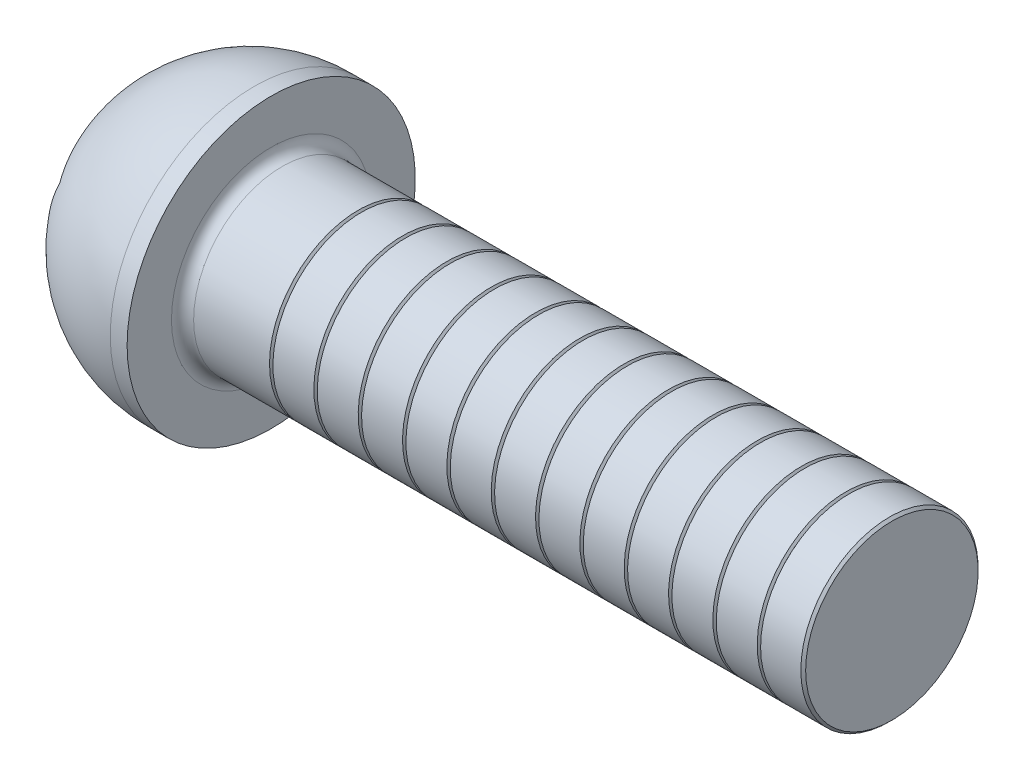
SolidWorks part; units mm, degrees
ref_plane "Plane1" through (0, 0, 0) normal (0, 0, 1) x (1, 0, 0)
ref_plane "Plane2" through (0, 0, 0) normal (0, 1, 0) x (1, 0, 0)
ref_plane "Plane3" through (0, 0, 0) normal (1, 0, 0) x (0, 0, -1)
sketch "BodySke" plane through (0, 0, 0) normal (0, 0, 1) x (1, 0, 0)
  line L0 (17.3, 0) -> (17.3, 1.9455)
  line L1 (17.2455, 2) -> (3.3, 2)
  line L2 (3.3, 2) -> (3.3, 3.25)
  line L3 (3.3, 3.25) -> (2.92, 3.25)
  line L4 (0, 0) -> (101.6, 0) construction
  line L5 (3.3, -3.25) -> (2.92, -3.25) construction
  line L6 (55.6768, -2) -> (3.3, -2) construction
  line L7 (17.3, 0) -> (0, 0)
  line L8 (0, 1.625) -> (0, -1.625) construction
  line L9 (0, 0) -> (0, 1.625)
  line L10 (17.3, 1.9455) -> (17.2455, 2)
  line L11 (17.3, -1.9455) -> (17.2455, -2) construction
  line L12 (4.3, 9.525) -> (4.3, -2) construction
  line L13 (5.3, 9.525) -> (5.3, -2) construction
  arc A1 (0, 1.625) -> (2.92, 3.25) centre (2.8165, 0) cw
  dimension "Diameter" = 4
  dimension "Length" = 14
  dimension "Head_dia" = 6.5
  dimension "D1" = 3.25
  dimension "Head_ht" = 3.3
  dimension "Head_side_ht" = 0.38
  dimension "Minor_dia" = 3.891
  dimension "Body_ch_ang" = 45
  dimension "Advance" = 1
  dimension "Thread_nom" = 12
revolve "BaseBody" add sketch "BodySke" angle 360 about L4
cosmetic thread "ThreadCosmetic" [suppressed] parameters "Thread_length"=12, "Thread_minor"=3.891
fillet "Fillet1" radius 0.25 1 edges at (3.3, 0, 2)
sketch "Sketch2" plane through (0, 0, 0) normal (0, 0, 1) x (1, 0, 0)
  line L0 (0, 2) -> (2.08, 2)
  line L1 (2.08, 2) -> (3.2347, 0)
  line L3 (3.2347, 0) -> (0, 0)
  line L4 (0, 0) -> (0, 2)
  line L5 (0, -2) -> (2.08, -2) construction
  line L6 (0, 0) -> (47.625, 0) construction
  dimension "D2" = 60
  dimension "PreBroach_depth" = 2.08
  dimension "PreBroach_dia" = 4
revolve "PreBroach" cut sketch "Sketch2" angle 360 about L6
sketch "Sketch3" plane through (0, 0, 0) normal (1, 0, 0) x (0, 0, -1)
  line L0 (-2, -1.1547) -> (-2, 1.1547)
  line L1 (-2, 1.1547) -> (0, 2.3094)
  line L2 (0, 2.3094) -> (2, 1.1547)
  line L3 (2, 1.1547) -> (2, -1.1547)
  line L4 (2, -1.1547) -> (0, -2.3094)
  line L5 (0, -2.3094) -> (-2, -1.1547)
  dimension "Hex_size" = 4
  dimension "D3" = 4
  dimension "D1" = 2
  dimension "D2" = 2
extrude "Hex" cut sketch "Sketch3" along normal blind 2.08
sketch "ThdSchSke" plane through (0, 0, 0) normal (0, 0, 1) x (1, 0, 0)
  line L0 (5.3, -1.9455) -> (5.2618, -2)
  line L1 (5.3, -1.9455) -> (5.3382, -2)
  line L2 (5.3382, -2) -> (5.3382, -2.5)
  line L3 (-3.175, 0) -> (5.1513, 0) construction
  line L5 (5.3382, -2.5) -> (5.2618, -2.5)
  line L6 (5.2618, -2.5) -> (5.2618, -2)
  dimension "Diameter" = 4
  dimension "Thread_minor" = 3.891
  dimension "SideAngle" = 55
  dimension "VeeAngle" = 70
  dimension "Overcut" = 5
  dimension "Start" = 5.3
revolve "ThreadSchematic" cut sketch "ThdSchSke" angle 360 about L3
pattern_linear "ThdSchPat" count 12 spacing 1 along (1, 0, 0) of "ThreadSchematic"
equation "\"D1@BodySke\" = \"Head_dia@BodySke\" * .5"
equation "\"Thread_minor@ThreadCosmetic\" = \"Minor_dia@BodySke\""
equation "\"D1@Sketch3\" = \"Hex_size@Sketch3\" / 2"
equation "\"D2@Sketch3\" = \"D1@Sketch3\""
equation "\"D3@Sketch3\" = \"Hex_size@Sketch3\""
equation "\"Thread_length@ThreadCosmetic\" = ((sgn( (\"Length@BodySke\" - \"Advance@BodySke\" * 2.0) - \"Thread_nom@BodySke\" )-1)*( (\"Length@BodySke\" - \"Advance@BodySke\" * 2.0) - \"Thread_nom@BodySke\" ))/-2+ \"Thread_nom@BodySke\""
equation "\"Thread_minor@ThdSchSke\" = \"Minor_dia@BodySke\""
equation "\"Diameter@ThdSchSke\" = \"Diameter@BodySke\""
equation "\"Overcut@ThdSchSke\" = \"Diameter@BodySke\" * 1.25"
equation "\"Start@ThdSchSke\" = \"Head_ht@BodySke\" + \"Length@BodySke\" - \"Thread_length@ThreadCosmetic\"  '---Non-countersunk---"
equation "\"Num_threads@ThdSchPat\" = int( \"Thread_length@ThreadCosmetic\" / \"Advance@BodySke\" + 0.999 )  + 1"
equation "\"Advance@ThdSchPat\" = \"Thread_length@ThreadCosmetic\" /  (\"Num_threads@ThdSchPat\" - 1) 'relax it"
equation "\"Num_threads@ThdSchPat\" = \"Num_threads@ThdSchPat\" - sgn( \"Num_threads@ThdSchPat\" - 1) '---chamfered tips only---"
